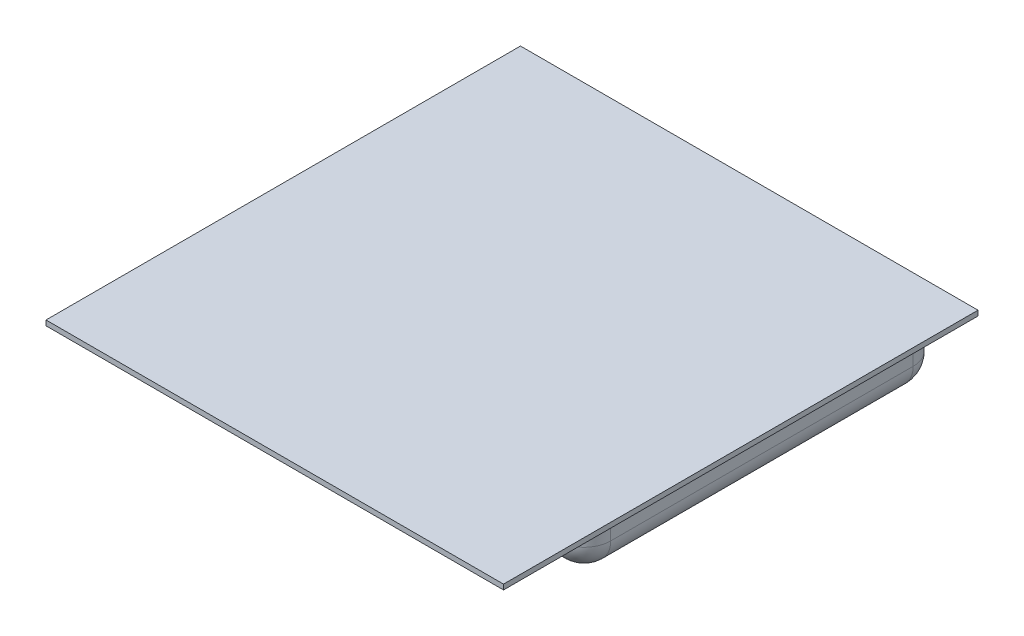
SolidWorks part; units mm, degrees
ref_plane "Front Plane" through (0, 0, 0) normal (0, 0, 1) x (1, 0, 0)
ref_plane "Top Plane" through (0, 0, 0) normal (0, 1, 0) x (1, 0, 0)
ref_plane "Right Plane" through (0, 0, 0) normal (1, 0, 0) x (0, 0, -1)
sketch "Sketch1" plane through (0, 0, 0) normal (0, 0, 1) x (1, 0, 0)
  line L0 (0, 0) -> (0, 52.3444) construction
  line L2 (-85.725, 1.905) -> (85.725, 1.905)
  line L3 (-85.725, 1.905) -> (-85.725, 0)
  line L4 (-85.725, 0) -> (85.725, 0)
  line L5 (85.725, 1.905) -> (85.725, 0)
  dimension "D1" = 1.905
  dimension "D2" = 171.45
extrude "Extrude1" add sketch "Sketch1" along normal mid plane 177.8
sketch "Sketch2" plane through (0, 0, 0) normal (0, -1, 0) x (1, 0, 0)
  line L0 (-85.725, 88.9) -> (85.725, 88.9) construction
  line L1 (-77.7875, 50.8) -> (77.7875, 50.8)
  line L2 (-77.7875, 50.8) -> (-77.7875, -82.55)
  line L3 (-77.7875, -82.55) -> (77.7875, -82.55)
  line L4 (77.7875, 50.8) -> (77.7875, -82.55)
  line L5 (0, 50.8) -> (0, 0) construction
  dimension "D1" = 38.1
  dimension "D2" = 155.575
  dimension "D3" = 133.35
extrude "Extrude2" add sketch "Sketch2" along normal blind 22.1
fillet "Fillet1" radius 10 4 edges at (-77.7875, -11.05, -82.55) (77.7875, -11.05, -82.55) (77.7875, -11.05, 50.8) (-77.7875, -11.05, 50.8)
fillet "Fillet2" radius 10 8 edges at (-74.8586, -22.1, 47.8711) (0, -22.1, 50.8) (74.8586, -22.1, 47.8711) (77.7875, -22.1, -15.875) (74.8586, -22.1, -79.6211) (0, -22.1, -82.55) (-74.8586, -22.1, -79.6211) (-77.7875, -22.1, -15.875)
